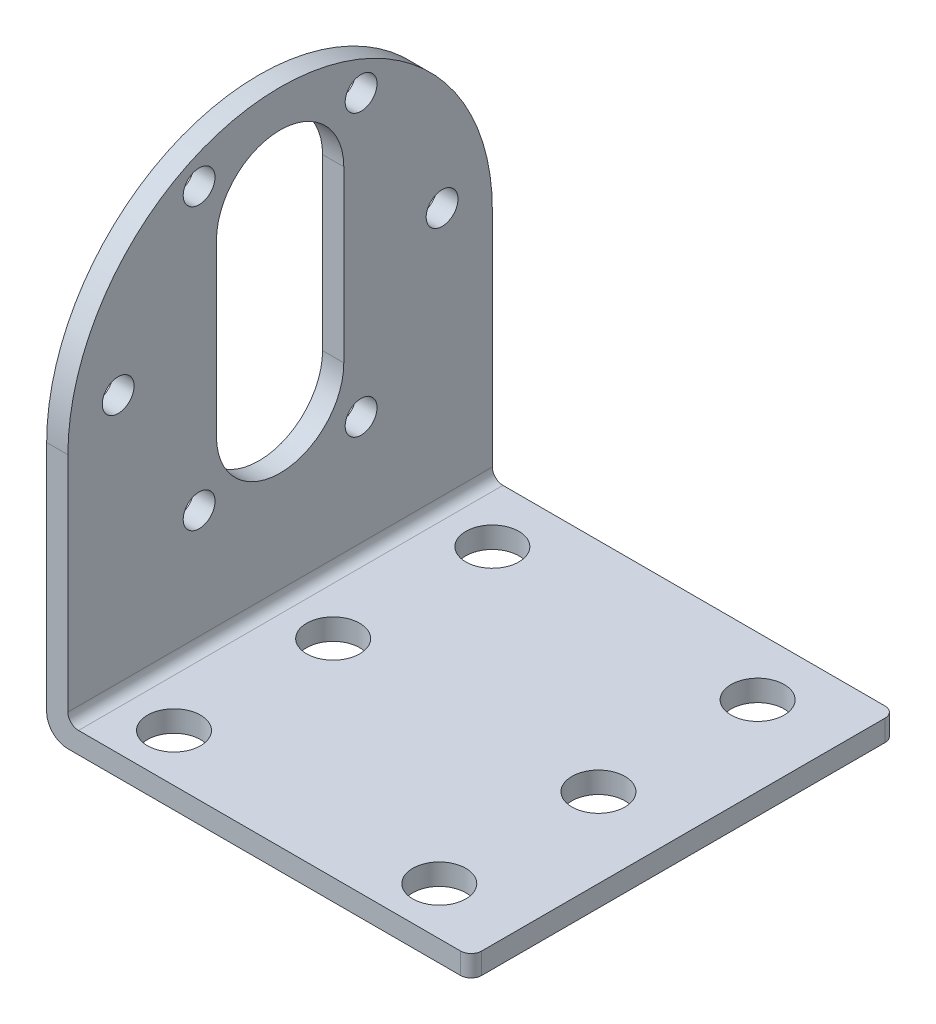
SolidWorks part; units mm, degrees
material "Alloy Steel (SS)"
ref_plane "Front Plane" through (0, 0, 0) normal (0, 0, 1) x (1, 0, 0)
ref_plane "Top Plane" through (0, 0, 0) normal (0, 1, 0) x (1, 0, 0)
ref_plane "Right Plane" through (0, 0, 0) normal (1, 0, 0) x (0, 0, -1)
sketch "Sketch2" plane through (0, 0, 0) normal (0, 0, 1) x (1, 0, 0)
  line L0 (2, 0) -> (40, 0)
  line L1 (0, 2) -> (0, 45)
  line L2 (2, 3) -> (2, 45)
  line L3 (3, 2) -> (40, 2)
  line L4 (40, 2) -> (40, 0)
  line L5 (0, 45) -> (2, 45)
  line L6 (2, 2) -> (40, 2) construction
  line L7 (2, 2) -> (2, 45) construction
  line L8 (0, 0) -> (40, 0) construction
  line L9 (0, 0) -> (0, 45) construction
  arc A0 (3, 2) -> (2, 3) centre (3, 3) cw
  arc A1 (2, 0) -> (0, 2) centre (2, 2) cw
  point P13 (0, 0)
  dimension "D4" = 1
  dimension "D5" = 2
  dimension "D1" = 40
  dimension "D3" = 45
  dimension "D2" = 2
extrude "Boss-Extrude1" add sketch "Sketch2" along normal blind 40
sketch "Sketch3" plane through (0, 2, 0) normal (0, 1, 0) x (1, 0, 0)
  line L0 (40, -40) -> (3, -40) construction
  point P0 (32.5, -35.5)
  point P6 (32.5, -5.5)
  point P9 (7.5, -5.5)
  point P11 (7.5, -35.5)
  dimension "D1" = 4.5
  dimension "D2" = 7.5
  dimension "D3" = 30
  dimension "D4" = 25
hole_wizard "Hole1" positions "Sketch3" profile "Sketch4" legacy end condition through all
sketch "Sketch4" plane through (32.5, 2, 35.5) normal (1, 0, 0) x (0, 0, 1)
  line L0 (0, 0) -> (0, 2)
  line L1 (0, 2) -> (2.5, 2)
  line L2 (2.5, 2) -> (2.5, 0)
  line L3 (2.5, 0) -> (0, 0)
  line L4 (0, 110) -> (0, -10) construction
  dimension "Diameter" = 5
  dimension "Depth" = 2
sketch "Sketch5" plane through (2, 0, 0) normal (1, 0, 0) x (0, 0, -1)
  line L0 (-40, 3) -> (-40, 45) construction
  line L1 (-40, 3) -> (-40, 45)
  line L2 (0, 3) -> (0, 45) construction
  line L3 (0, 3) -> (0, 45)
  line L4 (-40, 24) -> (-40, 3)
  line L5 (0, 3) -> (0, 24)
  arc A0 (-40, 24) -> (0, 24) centre (-20, 24) cw
  line M2 (0, 45) -> (-40, 45)
  line M3 (-40, 45) -> (-40, 3)
  dimension "D1" = 20
extrude "Cut-Extrude1" cut sketch "Sketch5" against normal blind 40 contours A0 L3 M3 M2
sketch "Sketch6" plane through (2, 0, 0) normal (1, 0, 0) x (0, 0, -1)
  line L0 (-20, 34.5) -> (-20, 18.5) construction
  line L1 (-14, 34.5) -> (-14, 18.5)
  line L2 (-26, 34.5) -> (-26, 18.5)
  arc A0 (-14, 34.5) -> (-26, 34.5) centre (-20, 34.5) ccw
  arc A1 (-26, 18.5) -> (-14, 18.5) centre (-20, 18.5) ccw
  arc A2 (0, 24) -> (-40, 24) centre (-20, 24) ccw construction
  circle A3 centre (-20, 26.5) radius 15 construction
  point P3 (-20, 26.5)
  point P8 (-20, 40.5)
  point P9 (-20, 12.5)
  point P13 (-20, 44)
  dimension "D3" = 6
  dimension "D4" = 30
  dimension "D1" = 28
  dimension "D2" = 9.5
extrude "Cut-Extrude2" cut sketch "Sketch6" against normal blind 40
sketch "Sketch7" plane through (2, 0, 0) normal (1, 0, 0) x (0, 0, -1)
  line L0 (-20, 40.5) -> (-20, 12.5) construction
  line L1 (-35.265, 26.5) -> (-20, 26.5) construction
  line L2 (-20, 26.5) -> (-27.6325, 13.2801) construction
  arc A0 (-14, 34.5) -> (-26, 34.5) centre (-20, 34.5) ccw construction
  arc A1 (-26, 18.5) -> (-14, 18.5) centre (-20, 18.5) ccw construction
  circle A2 centre (-20, 26.5) radius 15.265 construction
  circle A3 centre (-4.735, 26.5) radius 1.5
  circle A4 centre (-35.265, 26.5) radius 1.5
  circle A5 centre (-27.6325, 13.2801) radius 1.5
  circle A6 centre (-12.3675, 13.2801) radius 1.5
  circle A7 centre (-27.6325, 39.7199) radius 1.5
  circle A8 centre (-12.3675, 39.7199) radius 1.5
  dimension "D1" = 30.53
  dimension "D2" = 3
  dimension "D3" = 3
  dimension "D4" = 3
  dimension "D6" = 3
  dimension "D7" = 3
  dimension "D8" = 3
  dimension "D5" = 60
extrude "Cut-Extrude3" cut sketch "Sketch7" against normal blind 40
fillet "Fillet1" radius 1 2 edges at (40, 1, 0) (40, 1, 40)
sketch "Sketch10" plane through (0, 2, 0) normal (0, 1, 0) x (1, 0, 0)
  line L0 (7.5, -3) -> (7.5, -38) construction
  line L1 (32.5, -3) -> (32.5, -38) construction
  circle A0 centre (7.5, -5.5) radius 2.5 construction
  circle A1 centre (7.5, -35.5) radius 2.5 construction
  circle A2 centre (32.5, -5.5) radius 2.5 construction
  circle A3 centre (32.5, -35.5) radius 2.5 construction
  circle A4 centre (7.5, -20.5) radius 2.5
  circle A5 centre (32.5, -20.5) radius 2.5
  dimension "D1" = 5
  dimension "D2" = 5
extrude "Cut-Extrude4" cut sketch "Sketch10" against normal blind 40
